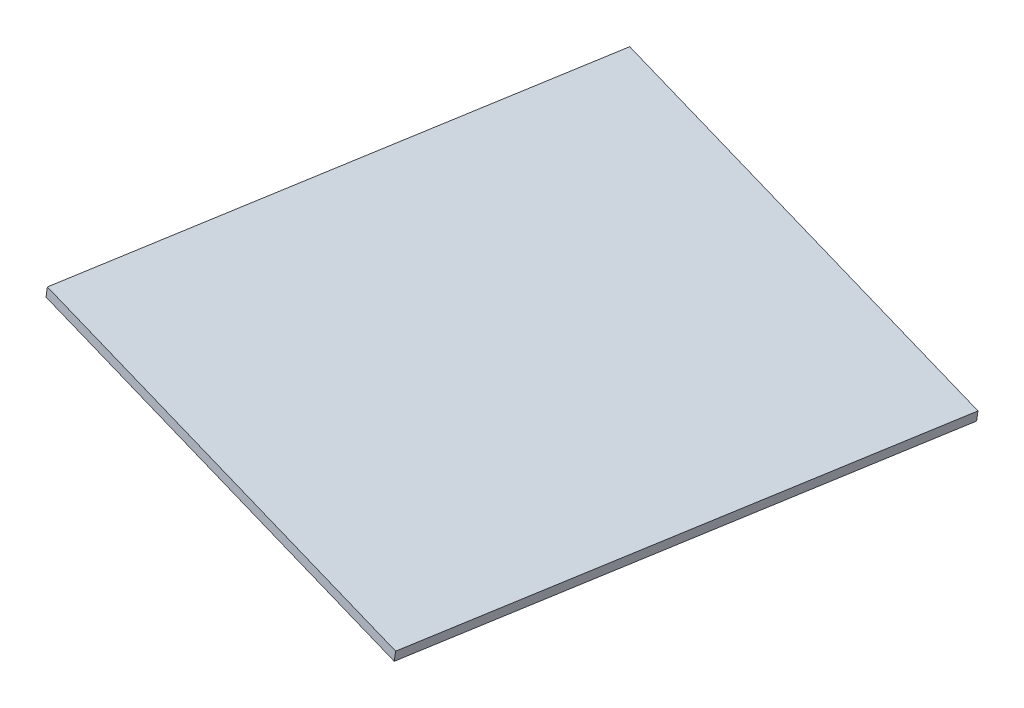
SolidWorks part; units mm, degrees
other "Markup1"
sketch "Sketch8" plane through (257.7307, 430.8513, 260.066) normal (0.119, 0.9518, 0.2826) x (0.9929, -0.114, -0.0339)
ref_plane "Front Plane" through (0, 0, 0) normal (0, 0, 1) x (1, 0, 0)
ref_plane "Top Plane" through (0, 0, 0) normal (0, 1, 0) x (1, 0, 0)
ref_plane "Right Plane" through (0, 0, 0) normal (1, 0, 0) x (0, 0, -1)
sketch "Sketch1" plane through (492.5318, 3075.3764, 146.8321) normal (-0.1672, -0.9856, -0.0259) x (0.9409, -0.1673, 0.2944)
  line L13 (21.508, 701.2072) -> (150.2759, 683.3512)
  line L19 (21.508, 701.2072) -> (0.4076, 549.0411)
  line L21 (150.2759, 683.3512) -> (129.1754, 531.1851)
  line L22 (0.4076, 549.0411) -> (129.1754, 531.1851)
  line L23 (29.949, 762.0794) -> (-8.762, 482.9147) construction
  line L24 (158.7169, 744.2235) -> (120.0059, 465.0588) construction
  line L27 (26.4607, 700.5204) -> (21.508, 701.2072) construction
  line L28 (188.4087, 522.9714) -> (-58.8257, 557.2548) construction
extrude "Boss-Extrude1" add sketch "Sketch1" against normal blind 3
